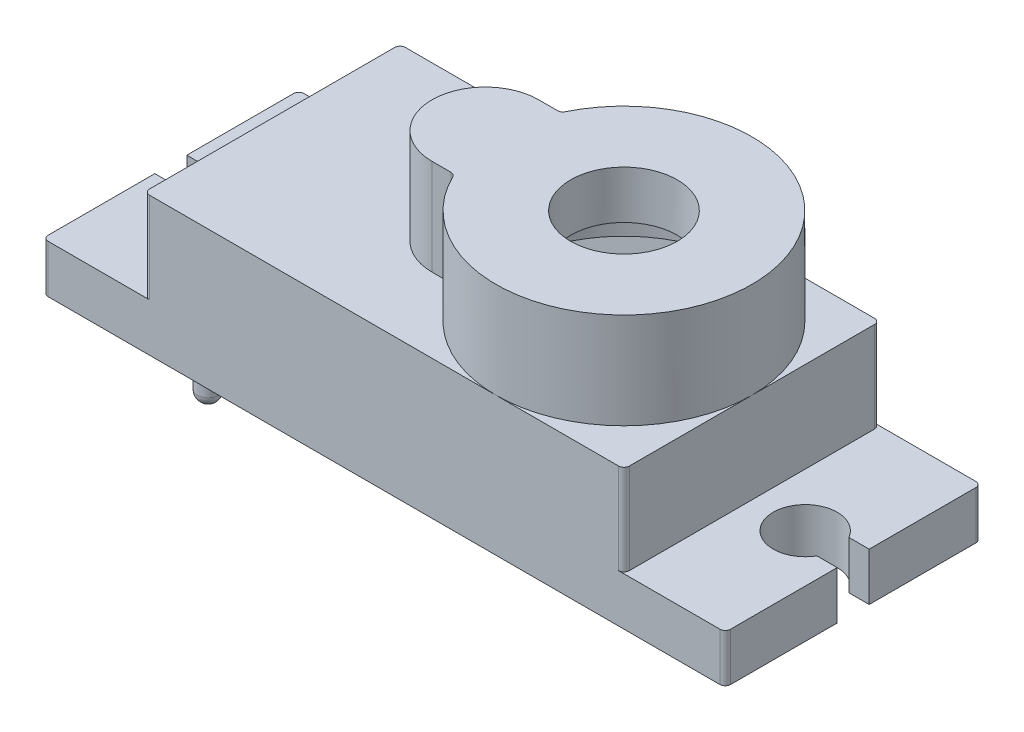
SolidWorks part; units mm, degrees
ref_plane "Front Plane" through (0, 0, 0) normal (0, 0, 1) x (1, 0, 0)
ref_plane "Top Plane" through (0, 0, 0) normal (0, 1, 0) x (1, 0, 0)
ref_plane "Right Plane" through (0, 0, 0) normal (1, 0, 0) x (0, 0, -1)
sketch "Sketch1" plane through (0, 0, 0) normal (0, 1, 0) x (1, 0, 0)
  line L0 (10.25, 5) -> (-10.25, 5)
  line L1 (11.25, -6) -> (-11.25, -6)
  line L2 (11.25, -6) -> (11.25, 6)
  line L3 (11.25, 6) -> (-11.25, 6)
  line L4 (-11.25, -6) -> (-11.25, 6)
  line L5 (11.25, -6) -> (-11.25, 6) construction
  line L6 (11.25, 6) -> (-11.25, -6) construction
  line L8 (10.25, -5) -> (-10.25, -5)
  line L10 (-10.25, -5) -> (-10.25, 5) construction
  line L11 (10.25, -5) -> (10.25, 5) construction
  line L12 (-10.75, 5) -> (-10.75, -5)
  line L13 (10.75, 5) -> (10.75, -5)
  line L14 (10.25, 5) -> (10.75, 5)
  line L15 (10.25, -5) -> (10.75, -5)
  line L16 (-10.75, -5) -> (-10.25, -5)
  line L17 (-10.75, 5) -> (-10.25, 5)
  point P0 (0, 0)
  dimension "D1" = 12
  dimension "D2" = 22.5
  dimension "D4" = 0.5
  dimension "D5" = 0.5
  dimension "D3" = 1
extrude "Boss-Extrude1" add sketch "Sketch1" along normal blind 6.5
sketch "Sketch2" plane through (0, 6.5, 0) normal (0, 1, 0) x (1, 0, 0)
  line L0 (0, 0) -> (-8.3918, 0) construction
  line L1 (11.25, -6) -> (-11.25, -6)
  line L2 (11.25, -6) -> (11.25, 6)
  line L3 (11.25, 6) -> (-11.25, 6)
  line L4 (-11.25, -6) -> (-11.25, 6)
  line L5 (11.25, -6) -> (-11.25, 6) construction
  line L6 (11.25, 6) -> (-11.25, -6) construction
  arc A0 (-0.2885, -2.3077) -> (-0.2885, 2.3077) centre (5.25, 0) ccw
  arc A1 (-0.2885, 2.3077) -> (-0.2885, -2.3077) centre (-1.25, 0) ccw
  point P0 (0, 0)
  dimension "D1" = 12
  dimension "D2" = 5
  dimension "D3" = 6.5
extrude "Boss-Extrude2" add sketch "Sketch2" against normal blind 0.5 contours L1 L4 L3 L2
sketch "Sketch3" plane through (0, 6.5, 0) normal (0, 1, 0) x (1, 0, 0)
  line L0 (-1.25, 2.5) -> (-0.2044, 2.5)
  line L1 (-1.25, -2.5) -> (-0.2044, -2.5)
  line L2 (-1.25, 0) -> (-1.25, 4.6186) construction
  line L3 (-1.25, 2.1) -> (0.0587, 2.1)
  line L4 (-1.25, -2.1) -> (0.0587, -2.1)
  arc A0 (-0.2885, 2.3077) -> (-0.2885, -2.3077) centre (-1.25, 0) ccw construction
  arc A1 (-0.2885, -2.3077) -> (-0.2885, 2.3077) centre (5.25, 0) ccw construction
  arc A2 (-1.25, 2.5) -> (-1.25, -2.5) centre (-1.25, 0) ccw
  arc A3 (-0.2044, -2.5) -> (-0.2044, 2.5) centre (5.25, 0) ccw
  arc A4 (0.0587, -2.1) -> (0.0587, 2.1) centre (5.25, 0) ccw
  arc A5 (-1.25, 2.1) -> (-1.25, -2.1) centre (-1.25, 0) ccw
  dimension "D1" = 0.4
extrude "Boss-Extrude3" add sketch "Sketch3" along normal blind 4.5
sketch "Sketch4" plane through (0, 11, 0) normal (0, 1, 0) x (1, 0, 0)
  line L0 (-1.25, -2.5) -> (-0.2044, -2.5) construction
  line L1 (-1.25, 2.5) -> (-0.2044, 2.5) construction
  line L2 (-1.25, -2.5) -> (-0.2044, -2.5)
  line L3 (-1.25, 2.5) -> (-0.2044, 2.5)
  arc A0 (-0.2044, -2.5) -> (-0.2044, 2.5) centre (5.25, 0) ccw construction
  arc A1 (-1.25, 2.5) -> (-1.25, -2.5) centre (-1.25, 0) ccw construction
  arc A2 (5.25, 6) -> (-0.2044, 2.5) centre (5.25, 0) ccw construction
  arc A3 (-0.2044, -2.5) -> (-0.2044, 2.5) centre (5.25, 0) ccw
  arc A4 (-1.25, 2.5) -> (-1.25, -2.5) centre (-1.25, 0) ccw
  arc A5 (5.25, 6) -> (-0.2044, 2.5) centre (5.25, 0) ccw
  circle A6 centre (5.25, 0) radius 2.5
  arc M5 (-1.25, -2.1) -> (-1.25, 2.1) centre (-1.25, 0) cw
  line M6 (-1.25, 2.1) -> (0.0587, 2.1)
  arc M7 (0.0587, 2.1) -> (0.0587, -2.1) centre (5.25, 0) cw
  line M8 (0.0587, -2.1) -> (-1.25, -2.1)
  dimension "D1" = 5
extrude "Boss-Extrude4" add sketch "Sketch4" against normal blind 1 contours A6 M5 M8 M7 M6
sketch "Sketch5" plane through (0, 6.5, 0) normal (0, 1, 0) x (1, 0, 0)
  line L0 (-1.25, -2.1) -> (0.0587, -2.1) construction
  line L1 (-1.25, 2.1) -> (0.0587, 2.1) construction
  line L2 (-1.25, -2.1) -> (0.0587, -2.1)
  line L3 (-1.25, 2.1) -> (0.0587, 2.1)
  arc A0 (-1.25, 2.1) -> (-1.25, -2.1) centre (-1.25, 0) ccw construction
  arc A1 (0.0587, -2.1) -> (0.0587, 2.1) centre (5.25, 0) ccw construction
  arc A2 (-1.25, 2.1) -> (-1.25, -2.1) centre (-1.25, 0) ccw
  arc A3 (0.0587, -2.1) -> (0.0587, 2.1) centre (5.25, 0) ccw
extrude "Cut-Extrude1" cut sketch "Sketch5" against normal through all
sketch "Sketch6" plane through (0, 10, 0) normal (0, -1, 0) x (1, 0, 0)
  circle A0 centre (5.25, 0) radius 2.5 construction
  circle A1 centre (5.25, 0) radius 2.5
  circle A2 centre (5.25, 0) radius 3
  dimension "D1" = 0.5
extrude "Boss-Extrude5" add sketch "Sketch6" along normal blind 1.25
sketch "Sketch7" plane through (0, 0, 0) normal (0, 1, 0) x (1, 0, 0)
  line L0 (0, 0) -> (0, 7.9309) construction
  line L1 (-11.25, 6) -> (-16, 6)
  line L2 (-11.25, 6) -> (-11.25, -6)
  line L3 (-11.25, -6) -> (-16, -6)
  line L4 (-16, 6) -> (-16, 0.75)
  line L5 (11.25, 6) -> (16, 6) construction
  line L6 (11.25, 6) -> (11.25, -6) construction
  line L7 (11.25, -6) -> (16, -6) construction
  line L8 (16, 6) -> (16, -6) construction
  line L9 (-15, 5) -> (-15, 1.4309)
  line L10 (-15, -5) -> (-11.5, -5)
  line L11 (-11.5, -5) -> (-11.5, 5)
  line L12 (-11.5, 5) -> (-15, 5)
  line L13 (-15, 0.75) -> (-16, 0.75)
  line L14 (-15, -0.75) -> (-16, -0.75)
  line L15 (-18.3674, 0) -> (-7.7299, 0) construction
  line L16 (-16, -0.75) -> (-16, -6)
  line L17 (-15, -1.4309) -> (-15, -5)
  line L19 (-15, 0.75) -> (-15.049, 0.75)
  line L20 (-15, -0.75) -> (-15.049, -0.75)
  arc A0 (-15.049, -0.75) -> (-15.049, 0.75) centre (-13.75, 0) ccw
  arc A1 (-15, -1.4309) -> (-15, 1.4309) centre (-13.75, 0) ccw
  circle A3 centre (-13.75, 0) radius 1.9 construction
  circle A4 centre (-13.75, 0) radius 1.5 construction
  point P20 (-12.0655, 0.4386)
  point P27 (-11.7787, 0.5263)
  dimension "D3" = 3
  dimension "D1" = 32
  dimension "D2" = 4.75
  dimension "D4" = 1
  dimension "D5" = 1
  dimension "D6" = 0.25
  dimension "D7" = 1
  dimension "D9" = 2.5
  dimension "D10" = 1.5
  dimension "D11" = 0.75
  dimension "D8" = 0.4
extrude "Boss-Extrude7" add sketch "Sketch7" along normal blind 2.25 contours A0 L14 L16 L3 L2 L1 L4 L13 L17 A1 L9 L12 L11 L10
sketch "Sketch8" plane through (0, 2.25, 0) normal (0, 1, 0) x (1, 0, 0)
  line L14 (-15.049, 0.75) -> (-16, 0.75) construction
  line L15 (-15.049, -0.75) -> (-16, -0.75) construction
  line L16 (-15.049, 0.75) -> (-16, 0.75)
  line L17 (-15.049, -0.75) -> (-16, -0.75)
  line L18 (-11.25, -6) -> (-11.25, 6)
  line L19 (-11.25, 6) -> (-16, 6)
  line L20 (-16, 6) -> (-16, 0.75)
  line L21 (-16, -0.75) -> (-16, -6)
  line L22 (-16, -6) -> (-11.25, -6)
  arc A2 (-15.049, -0.75) -> (-15.049, 0.75) centre (-13.75, 0) ccw construction
  arc A3 (-15.049, -0.75) -> (-15.049, 0.75) centre (-13.75, 0) ccw
extrude "Boss-Extrude8" add sketch "Sketch8" against normal blind 1
mirror "Mirror1" about plane through (0, 0, 0) normal (1, 0, 0) of "Boss-Extrude8", "Boss-Extrude7"
sketch "Sketch9" plane through (0, 10, 0) normal (0, -1, 0) x (1, 0, 0)
  circle A0 centre (-1.25, 0) radius 0.625
  arc A1 (-1.25, 2.1) -> (-1.25, -2.1) centre (-1.25, 0) ccw construction
  dimension "D1" = 1.25
extrude "Cut-Extrude2" cut sketch "Sketch9" against normal blind 0.25
sketch "Sketch11" plane through (0, 6, 0) normal (0, -1, 0) x (1, 0, 0)
  line L0 (-9.1712, 4.5) -> (-11.3288, 4.5) construction
  line L1 (-10.75, 5) -> (2.7281, 5) construction
  line L2 (-2.351, 0) -> (4.2132, 0) construction
  line L3 (0, 3.4177) -> (0, -3.002) construction
  line L6 (-11.5, 5) -> (-11.5, -5) construction
  circle A0 centre (-9.75, 4.5) radius 1.125
  circle A1 centre (-9.75, 4.5) radius 0.5 construction
  circle A2 centre (-9.75, -4.5) radius 0.5
  circle A3 centre (-9.75, -4.5) radius 1.125
  circle A4 centre (9.75, -4.5) radius 0.5 construction
  circle A5 centre (9.75, -4.5) radius 1.125
  circle A6 centre (9.75, 4.5) radius 1.125
  circle A7 centre (9.75, 4.5) radius 0.5
  point P21 (-10.25, 4.5)
  dimension "D1" = 2.25
  dimension "D2" = 1
  dimension "D3" = 1.25
extrude "Boss-Extrude9" add sketch "Sketch11" along normal up to surface (6 mm away) up to face at (0, 0, 0)
sketch "Sketch12" plane through (0, 0, 0) normal (0, -1, 0) x (1, 0, 0)
  circle A0 centre (-9.75, 4.5) radius 0.5
  circle A1 centre (9.75, -4.5) radius 0.5
  arc A2 (-10.75, 3.9846) -> (-8.7422, 5) centre (-9.75, 4.5) ccw construction
  arc A3 (10.75, -3.9846) -> (8.7422, -5) centre (9.75, -4.5) ccw construction
  dimension "D1" = 1
  dimension "D2" = 1
extrude "Boss-Extrude10" add sketch "Sketch12" along normal blind 2
fillet "Fillet1" radius 0.5 2 edges at (9.75, -2, -5) (-9.75, -2, 4)
fillet "Fillet2" radius 0.25 10 edges at (-0.2044, 8.75, -2.5) (-0.2044, 8.75, 2.5) (16, 1.125, 6) (16, 1.125, -6) (-16, 1.125, 6) (-16, 1.125, -6) (-11.25, 4.375, -6) (-11.25, 4.375, 6) (11.25, 4.375, -6) (11.25, 4.375, 6)
sketch "Sketch13" plane through (0, 0, 0) normal (0, -1, 0) x (1, 0, 0)
  line L0 (0.0587, 2.1) -> (0.0587, -2.1)
  arc A0 (0.0587, -2.1) -> (0.0587, 2.1) centre (5.25, 0) ccw construction
  arc A1 (0.0587, -2.1) -> (0.0587, 2.1) centre (5.25, 0) ccw
extrude "Cut-Extrude3" cut sketch "Sketch13" against normal up to surface (6 mm away) up to face at (-3.753, 6, 0)
